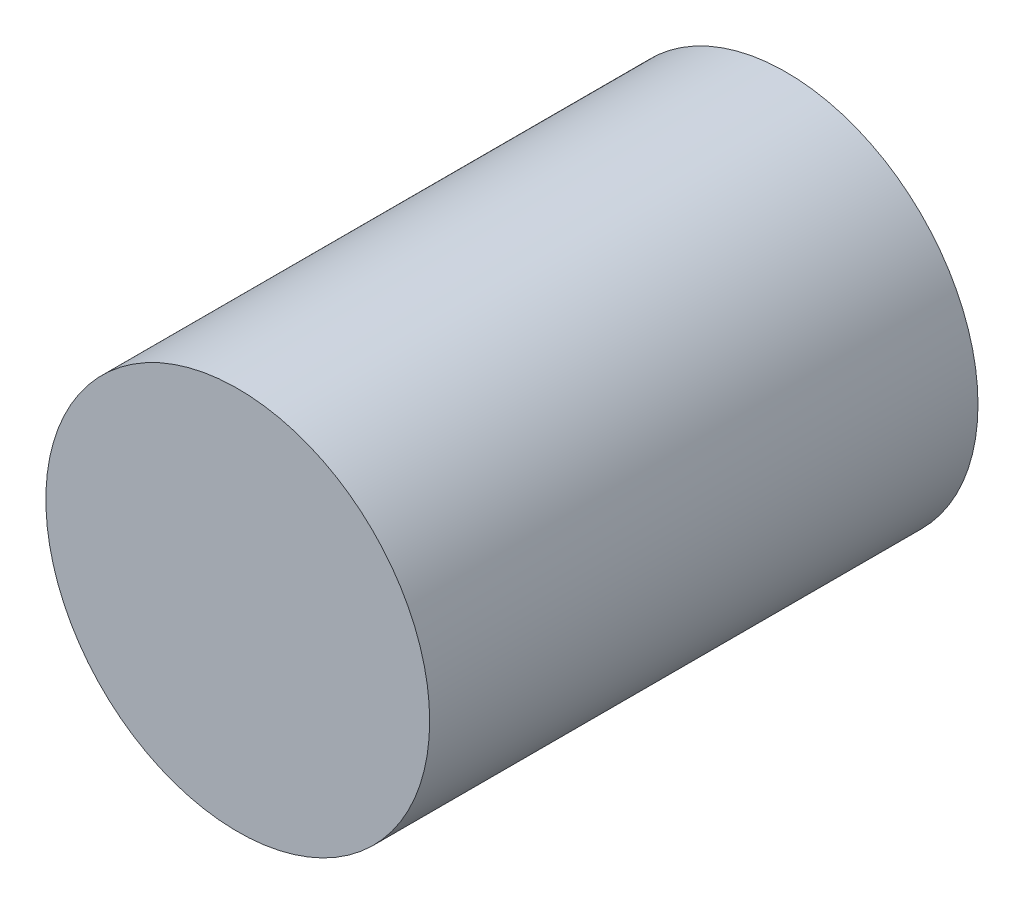
SolidWorks part; units mm, degrees
ref_plane "Ön Düzlem" through (0, 0, 0) normal (0, 0, 1) x (1, 0, 0)
ref_plane "Üst Düzlem" through (0, 0, 0) normal (0, 1, 0) x (1, 0, 0)
ref_plane "Sağ Düzlem" through (0, 0, 0) normal (1, 0, 0) x (0, 0, -1)
sketch "Çizim1" plane through (0, 0, 0) normal (0, 0, 1) x (1, 0, 0)
  circle A0 centre (0, 0) radius 4.445
  dimension "D1" = 8.89
extrude "Yükseklik-Ekstrüzyon1" add sketch "Çizim1" along normal blind 12.7
